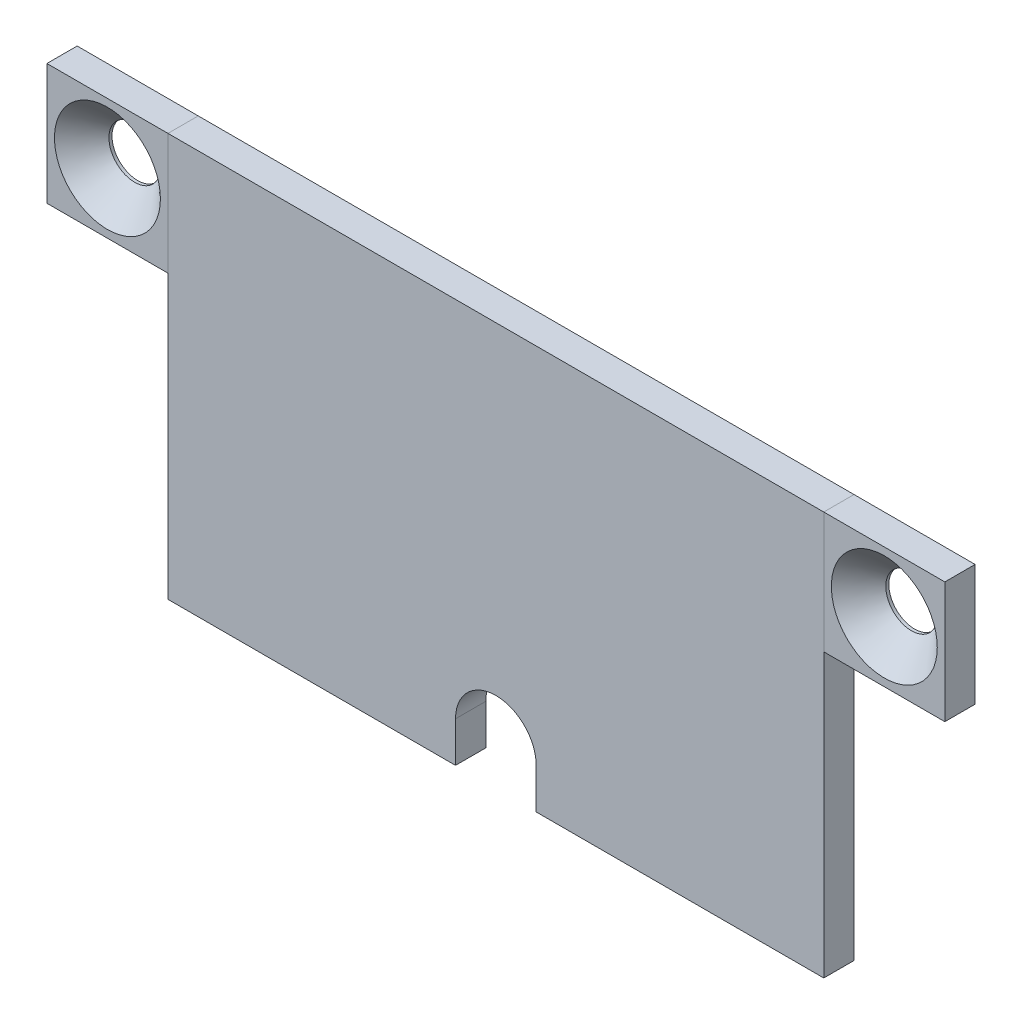
SolidWorks part; units mm, degrees
ref_plane "Plan de face" through (0, 0, 0) normal (0, 0, 1) x (1, 0, 0)
ref_plane "Plan de dessus" through (0, 0, 0) normal (0, 1, 0) x (1, 0, 0)
ref_plane "Plan de droite" through (0, 0, 0) normal (1, 0, 0) x (0, 0, -1)
sketch "Esquisse1" plane through (0, 0, 0) normal (0, 0, 1) x (1, 0, 0)
  line L1 (-34.9056, 53.1629) -> (30.0944, 53.1629)
  line L2 (-34.9056, 53.1629) -> (-34.9056, 13.1629)
  line L3 (-34.9056, 13.1629) -> (30.0944, 13.1629)
  line L4 (30.0944, 53.1629) -> (30.0944, 13.1629)
  dimension "D1" = 65
  dimension "D2" = 40
extrude "Boss.-Extru.1" add sketch "Esquisse1" along normal blind 3
sketch "Esquisse2" plane through (0, 0, 3) normal (0, 0, 1) x (1, 0, 0)
  line L1 (-34.9056, 53.1629) -> (-46.9056, 53.1629)
  line L2 (-34.9056, 53.1629) -> (-34.9056, 41.1629)
  line L3 (-34.9056, 41.1629) -> (-46.9056, 41.1629)
  line L4 (-46.9056, 53.1629) -> (-46.9056, 41.1629)
  line L5 (30.0944, 53.1629) -> (42.0944, 53.1629)
  line L6 (30.0944, 53.1629) -> (30.0944, 41.1629)
  line L7 (30.0944, 41.1629) -> (42.0944, 41.1629)
  line L8 (42.0944, 53.1629) -> (42.0944, 41.1629)
  dimension "D1" = 12
  dimension "D2" = 12
  dimension "D3" = 12
  dimension "D4" = 12
extrude "Boss.-Extru.2" add sketch "Esquisse2" against normal blind 3 separate body
sketch "Esquisse4" plane through (0, 0, 3) normal (0, 0, 1) x (1, 0, 0)
  line L1 (-34.9056, 13.1629) -> (30.0944, 13.1629) construction
  line L3 (-6.4056, 17.1629) -> (-6.4056, 13.1629)
  line L4 (-6.4056, 13.1629) -> (1.5944, 13.1629)
  line L5 (1.5944, 17.1629) -> (1.5944, 13.1629)
  line L6 (-34.9056, 53.1629) -> (-34.9056, 13.1629) construction
  arc A0 (-6.4056, 17.1629) -> (1.5944, 17.1629) centre (-2.4056, 17.1629) cw
  point P3 (-2.4056, 13.1629)
  point P10 (-30.6424, 13.3888)
  dimension "D1" = 4
  dimension "D2" = 4
  dimension "D3" = 0
  dimension "D4" = 32.5
extrude "Enlèv. mat.-Extru.1" cut sketch "Esquisse4" against normal through all
sketch "Esquisse5" plane through (0, 0, 3) normal (0, 0, 1) x (1, 0, 0)
  line L0 (-46.9056, 53.1629) -> (-46.9056, 41.1629) construction
  line L1 (-34.9056, 53.1629) -> (-46.9056, 53.1629) construction
  line L2 (42.0944, 41.1629) -> (42.0944, 53.1629) construction
  line L3 (42.0944, 53.1629) -> (30.0944, 53.1629) construction
  circle A0 centre (-40.9056, 47.1629) radius 5.25
  circle A1 centre (36.0944, 47.1629) radius 5.25
  dimension "D1" = 10.5
  dimension "D6" = 10.5
  dimension "D2" = 6
  dimension "D3" = 6
  dimension "D4" = 6
  dimension "D5" = 6
hole_wizard "Fraisage pour vis à tête fraisée bombée #51" positions "Esquisse3D1" profile "Esquisse6" countersink size "#5" standard "Ansi Inch" end condition through all
sketch3d "Esquisse3D1"
  point P0 (-40.9056, 47.1629, 3)
  point P3 (36.0944, 47.1629, 3)
sketch "Esquisse6" plane through (-40.9056, 47.1629, 3) normal (1, 0, 0) x (0, -1, 0)
  line L0 (0, 0) -> (0, 3)
  line L1 (0, 3) -> (2.55, 3)
  line L2 (2.55, 3) -> (2.55, 2.7)
  line L3 (2.55, 2.7) -> (5.25, 0)
  line L5 (5.25, 0) -> (0, 0)
  line L6 (-2.55, 2.7) -> (-5.25, 0) construction
  line L11 (0, -6.35) -> (0, 107.95) construction
  dimension "Diamètre du perçage jusqu'au prochain" = 5.1
  dimension "Profondeur du perçage jusqu'au prochain" = 3
  dimension "Diamètre du fraisage entrant" = 10.5
  dimension "Angle du fraisage entrant" = 90
